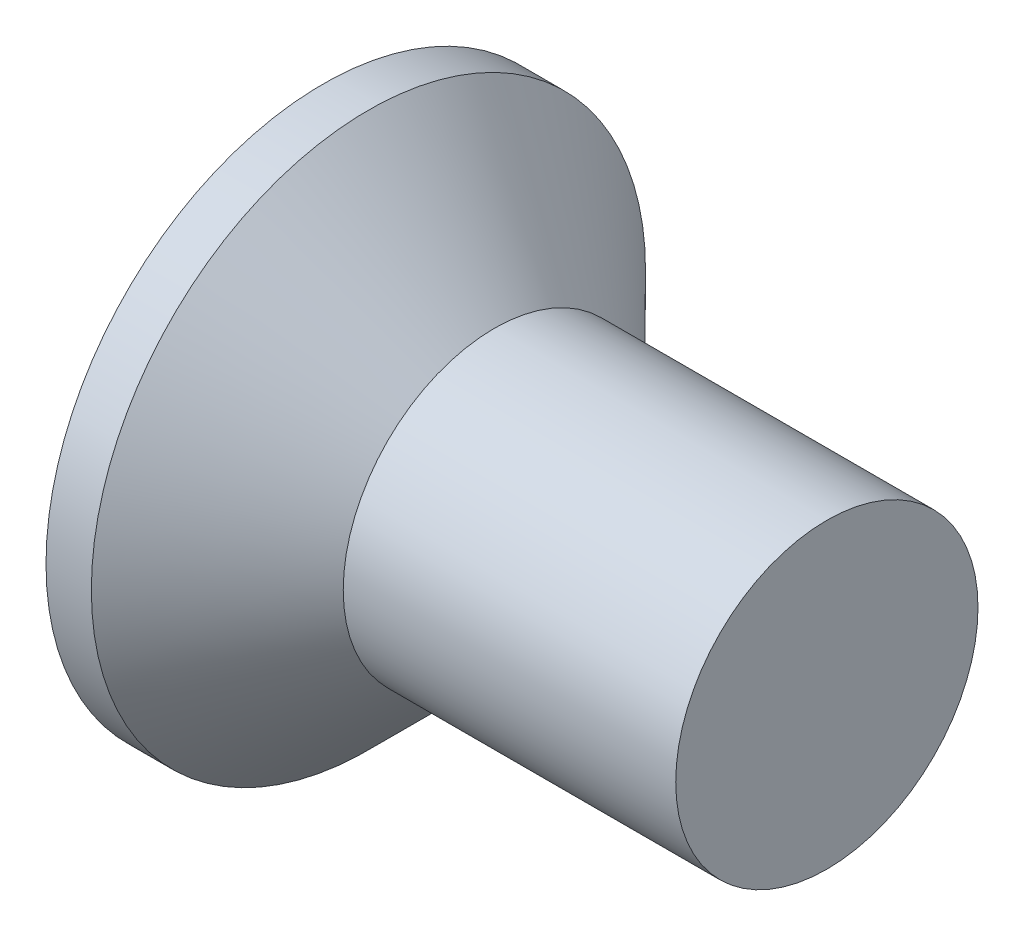
SolidWorks part; units mm, degrees
ref_plane "Plane1" through (0, 0, 0) normal (0, 0, 1) x (1, 0, 0)
ref_plane "Plane2" through (0, 0, 0) normal (0, 1, 0) x (1, 0, 0)
ref_plane "Plane3" through (0, 0, 0) normal (1, 0, 0) x (0, 0, -1)
sketch "BodySke" plane through (0, 0, 0) normal (0, 0, 1) x (1, 0, 0)
  line L0 (0, 0) -> (0, 2.75)
  line L1 (0, 2.75) -> (0.45, 2.75)
  line L2 (1.7, 1.5) -> (5, 1.5)
  line L3 (5, 1.5) -> (5, 0)
  line L4 (5, 0) -> (0, 0)
  line L5 (-6.35, 0) -> (82.55, 0) construction
  line L6 (1.7, -1.5) -> (5, -1.5) construction
  line L7 (0.45, -2.75) -> (1.7, -1.5) construction
  line L8 (0.45, 2.75) -> (1.7, 1.5)
  line L9 (0, -2.75) -> (0.45, -2.75) construction
  line L10 (2.2, 3.0875) -> (2.2, -6.4375) construction
  line L11 (0, 6.35) -> (0, -3.175) construction
  dimension "Diameter" = 3
  dimension "Length" = 5
  dimension "Head_ht" = 1.7
  dimension "Head_dia" = 5.5
  dimension "Head_ang" = 90
  dimension "D6" = 0.45
  dimension "Advance" = 0.5
  dimension "Thread_nom" = 5
revolve "Base-Revolve" add sketch "BodySke" angle 360 about L5
cosmetic thread "ThreadCosmetic" [suppressed] parameters "Thread_length"=2.8, "Thread_minor"=2.439
sketch "Sketch2" plane through (0, 0, 0) normal (-1, 0, 0) x (0, 0, 1)
  line L0 (-2.75, -0.5) -> (2.75, -0.5)
  line L1 (-2.75, -0.5) -> (-2.75, 0.5)
  line L2 (2.75, 0.5) -> (-2.75, 0.5)
  line L3 (2.75, 0.5) -> (2.75, -0.5)
  dimension "D1" = 0.5
  dimension "Slot_width" = 1
  dimension "D2" = 5.5
  dimension "D3" = 2.75
extrude "Slot" [suppressed] cut sketch "Sketch2" against normal blind 0.9
sketch "Sketch3" plane through (0, 0, 0) normal (-1, 0, 0) x (0, 0, 1)
  line L0 (-0.395, 1.55) -> (0.395, 1.55)
  line L1 (0.395, 1.55) -> (0.395, -1.55)
  line L2 (0.395, -1.55) -> (-0.395, -1.55)
  line L3 (-0.395, -1.55) -> (-0.395, 1.55)
  dimension "D1" = 1.55
  dimension "Cross_dia" = 3.1
  dimension "D2" = 0.395
  dimension "Cross_width" = 0.79
ref_plane "Plane4" through (2.08, 0, 0) normal (-1, 0, 0) x (0, 0, 1)
sketch "Sketch4" plane through (2.08, 0, 0) normal (-1, 0, 0) x (0, 0, 1)
  line L0 (-0.1975, 0.1975) -> (0.1975, 0.1975)
  line L3 (0.1975, 0.1975) -> (0.1975, -0.1975)
  line L4 (0.1975, -0.1975) -> (-0.1975, -0.1975)
  line L5 (-0.1975, -0.1975) -> (-0.1975, 0.1975)
  dimension "D1" = 0.395
  dimension "D2" = 0.395
  dimension "D3" = 0.1975
  dimension "D4" = 0.1975
loft "Cross" cut profiles "Sketch3", "Sketch4"
pattern_circular "CirPattern1" count 2 every 90 about axis through (0, 0, 0) along (1, 0, 0) of "Cross"
sketch "ThdSchSke" plane through (0, 0, 0) normal (0, 0, 1) x (1, 0, 0)
  line L0 (2.2, -1.2195) -> (2.0036, -1.5)
  line L1 (2.2, -1.2195) -> (2.3964, -1.5)
  line L2 (2.3964, -1.5) -> (2.3964, -1.875)
  line L3 (-3.175, 0) -> (5.1513, 0) construction
  line L5 (2.3964, -1.875) -> (2.0036, -1.875)
  line L6 (2.0036, -1.875) -> (2.0036, -1.5)
  line L7 (0, 2.75) -> (0, -2.75) construction
  dimension "Thread_minor" = 2.439
  dimension "Diameter" = 3
  dimension "Start" = 2.2
  dimension "SideAngle" = 55
  dimension "VeeAngle" = 70
  dimension "Overcut" = 3.75
revolve "ThreadSchematic" [suppressed] cut sketch "ThdSchSke" angle 360 about L3
pattern_linear "ThdSchPat" [suppressed]
equation "\"D1@Sketch3\" = \"Cross_dia@Sketch3\" / 2"
equation "\"D2@Sketch3\" = \"Cross_width@Sketch3\" / 2"
equation "\"D1@Sketch4\" = \"Cross_width@Sketch3\" *.5"
equation "\"D2@Sketch4\" = \"D1@Sketch4\""
equation "\"D4@Sketch4\" = \"D2@Sketch4\" / 2"
equation "\"D3@Sketch4\" = \"D1@Sketch4\" / 2"
equation "\"D1@Sketch2\" = \"Slot_width@Sketch2\" / 2"
equation "\"D2@Sketch2\" = \"Head_dia@BodySke\""
equation "\"D3@Sketch2\" = \"D2@Sketch2\" / 2"
equation "\"Thread_length@ThreadCosmetic\" = ((sgn( (\"Length@BodySke\" - \"Advance@BodySke\" - \"Head_ht@BodySke\" ) - \"Thread_nom@BodySke\" )-1)*( (\"Length@BodySke\" - \"Advance@BodySke\" - \"Head_ht@BodySke\" ) - \"Thread_nom@BodySke\" ))/-2+ \"Thread_nom@BodySke\""
equation "\"Thread_minor@ThdSchSke\" = \"Thread_minor@ThreadCosmetic\""
equation "\"Diameter@ThdSchSke\" = \"Diameter@BodySke\""
equation "\"Overcut@ThdSchSke\" = \"Diameter@BodySke\" * 1.25"
equation "\"Start@ThdSchSke\" = 0.000001 + \"Length@BodySke\" - \"Thread_length@ThreadCosmetic\"  '---Countersunk---"
equation "\"Num_threads@ThdSchPat\" = int( \"Thread_length@ThreadCosmetic\" / \"Advance@BodySke\" + 0.999 )  + 1"
equation "\"Advance@ThdSchPat\" = \"Thread_length@ThreadCosmetic\" /  (\"Num_threads@ThdSchPat\" - 1) 'relax it"
